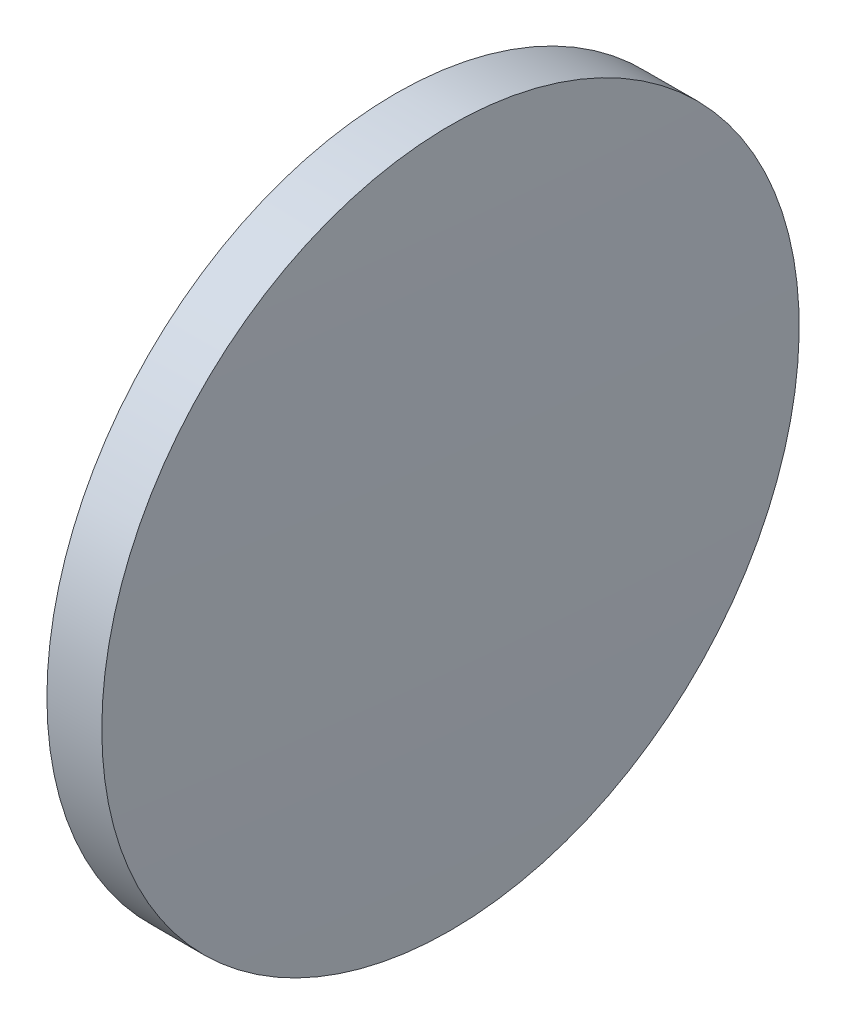
SolidWorks part; units mm, degrees
ref_plane "前视基准面" through (0, 0, 0) normal (0, 0, 1) x (1, 0, 0)
ref_plane "上视基准面" through (0, 0, 0) normal (0, 1, 0) x (1, 0, 0)
ref_plane "右视基准面" through (0, 0, 0) normal (1, 0, 0) x (0, 0, -1)
sketch "草图1" plane through (0, 0, 0) normal (0, 0, 1) x (1, 0, 0)
  line L0 (79.3054, 48.6161) -> (93.4772, 48.6161) construction
  line L1 (85.4585, 61.3161) -> (87.4579, 61.3161)
  line L2 (87.4579, 61.3161) -> (87.4579, 35.9161)
  line L3 (87.4579, 35.9161) -> (85.4585, 35.9161)
  line L4 (85.4585, 35.9161) -> (85.4585, 61.3161)
  arc A0 (85.4585, 61.3161) -> (85.4585, 35.9161) centre (621.9599, 48.6161) ccw
  arc A1 (87.4579, 35.9161) -> (87.4579, 61.3161) centre (-449.0435, 48.6161) ccw
  dimension "D1" = 25.4
  dimension "D2" = 1.9993
revolve "旋转1" add sketch "草图1" angle 360 about L0
